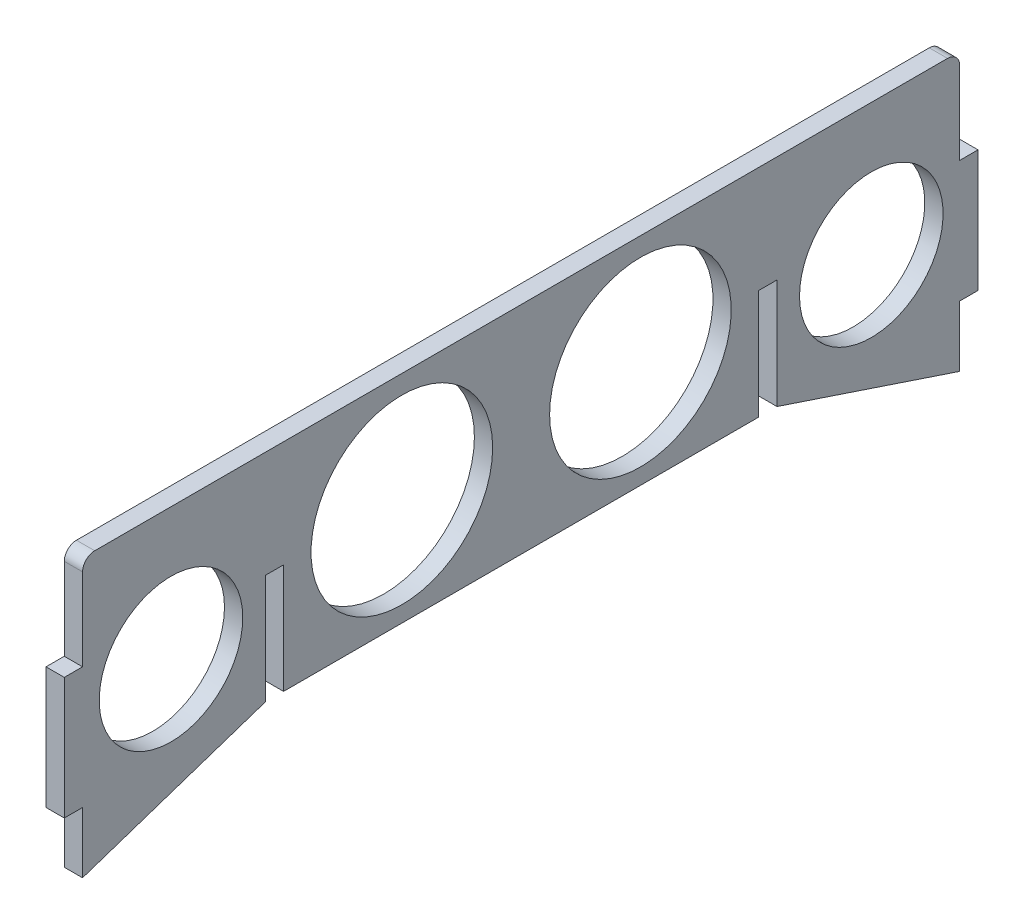
SolidWorks part; units mm, degrees
ref_plane "Front Plane" through (0, 0, 0) normal (0, 0, 1) x (1, 0, 0)
ref_plane "Top Plane" through (0, 0, 0) normal (0, 1, 0) x (1, 0, 0)
ref_plane "Right Plane" through (0, 0, 0) normal (1, 0, 0) x (0, 0, -1)
sketch "Sketch1" plane through (0, 0, 0) normal (1, 0, 0) x (0, 0, -1)
  line L1 (-72, -17.75) -> (72, -17.75)
  line L2 (-72, -17.75) -> (-72, 17.75)
  line L3 (-72, 17.75) -> (72, 17.75)
  line L4 (72, -17.75) -> (72, 17.75)
  line L5 (-72, -17.75) -> (72, 17.75) construction
  line L6 (-72, 17.75) -> (72, -17.75) construction
  point P0 (0, 0)
  dimension "D1" = 35.5
  dimension "D2" = 144
extrude "Boss-Extrude1" add sketch "Sketch1" along normal blind 3
fillet "Fillet1" radius 2 2 edges at (1.5, 17.75, -72) (1.5, 17.75, 72)
sketch "Sketch2" plane through (3, 0, 0) normal (1, 0, 0) x (0, 0, -1)
  line L0 (-72, -17.75) -> (72, -17.75) construction
  line L1 (-42, -17.75) -> (-39, -17.75)
  line L2 (-42, -17.75) -> (-42, 0.25)
  line L3 (-42, 0.25) -> (-39, 0.25)
  line L4 (-39, -17.75) -> (-39, 0.25)
  line L5 (-72, 15.75) -> (-72, -17.75) construction
  line L6 (0, 0) -> (0, -9.6726) construction
  line L7 (42, 0.25) -> (39, 0.25)
  line L8 (39, -17.75) -> (39, 0.25)
  line L9 (42, -17.75) -> (39, -17.75)
  line L10 (42, -17.75) -> (42, 0.25)
  dimension "D1" = 3
  dimension "D2" = 18
  dimension "D3" = 30
extrude "Cut-Extrude1" cut sketch "Sketch2" against normal blind 3
sketch "Sketch3" plane through (3, 0, 0) normal (1, 0, 0) x (0, 0, -1)
  line L0 (-72, -17.75) -> (-72, -27.75)
  line L1 (-72, -27.75) -> (-42, -17.75)
  line L2 (-72, -17.75) -> (-42, -17.75)
  dimension "D1" = 10
extrude "Boss-Extrude2" add sketch "Sketch3" against normal blind 3
mirror "Mirror1" about plane through (0, 0, 0) normal (0, 0, 1) of "Boss-Extrude2"
sketch "Sketch4" plane through (3, 0, 0) normal (1, 0, 0) x (0, 0, -1)
  line L0 (-72, 15.75) -> (-72, -27.75) construction
  line L1 (-72, -17.75) -> (-75, -17.75)
  line L2 (-72, -17.75) -> (-72, 2.25)
  line L3 (-72, 2.25) -> (-75, 2.25)
  line L4 (-75, -17.75) -> (-75, 2.25)
  line L5 (0, 1.65) -> (0, -1.65) construction
  line L6 (72, 2.25) -> (75, 2.25)
  line L7 (75, -17.75) -> (75, 2.25)
  line L8 (72, -17.75) -> (75, -17.75)
  line L9 (72, -17.75) -> (72, 2.25)
  dimension "D1" = 3
  dimension "D2" = 10
  dimension "D3" = 20
extrude "Boss-Extrude3" add sketch "Sketch4" against normal up to surface (3 mm away) up to face at (0, -4.1194, 0)
sketch "Sketch6" plane through (3, 0, 0) normal (1, 0, 0) x (0, 0, -1)
  line L0 (0, 1.65) -> (0, -1.65) construction
  circle A0 centre (-57.4831, -3.9089) radius 11.7828
  circle A1 centre (-19.5822, -0.2337) radius 14.9086
  circle A2 centre (57.4831, -3.9089) radius 11.7828
  circle A3 centre (19.5822, -0.2337) radius 14.9086
extrude "Cut-Extrude2" cut sketch "Sketch6" against normal blind 10
